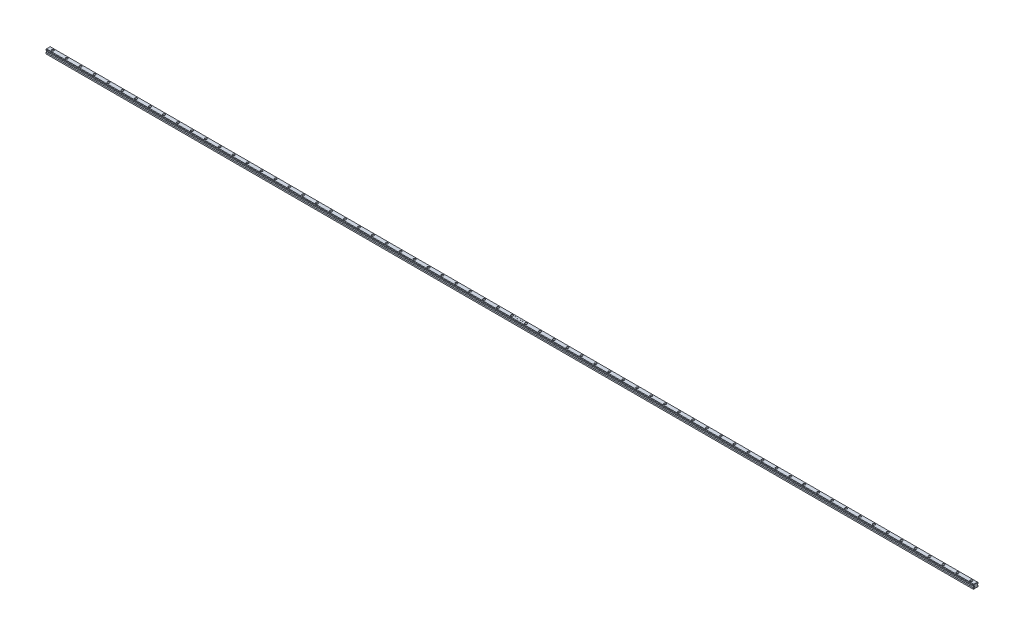
SolidWorks part; units mm, degrees
ref_plane "Front Plane" through (0, 0, 0) normal (0, 0, 1) x (1, 0, 0)
ref_plane "Top Plane" through (0, 0, 0) normal (0, 1, 0) x (1, 0, 0)
ref_plane "Right Plane" through (0, 0, 0) normal (1, 0, 0) x (0, 0, -1)
sketch "Sketch1" plane through (0, 0, 0) normal (1, 0, 0) x (0, 0, -1)
  line L0 (-10, 0) -> (10, 0)
  line L1 (-8, 18) -> (8, 18)
  line L2 (-10, 6) -> (-10, 0)
  line L3 (-8, 18) -> (-10, 16)
  line L4 (-10, 16) -> (-10, 13)
  line L5 (-10, 13) -> (-7, 10)
  line L6 (-7, 10) -> (-7, 8)
  line L7 (-7, 8) -> (-10, 6)
  line L8 (0, 0) -> (0, 18.5989) construction
  line L9 (-10, 18) -> (10, 18) construction
  line L10 (-10, 0) -> (10, 0) construction
  line L11 (10, 6) -> (10, 0)
  line L12 (7, 8) -> (10, 6)
  line L13 (7, 10) -> (7, 8)
  line L14 (10, 13) -> (7, 10)
  line L15 (10, 16) -> (10, 13)
  line L16 (8, 18) -> (10, 16)
  point P21 (0, 18)
  dimension "D3" = 6
  dimension "D4" = 2
  dimension "D5" = 2
  dimension "D6" = 3
  dimension "D7" = 3
  dimension "D8" = 2
  dimension "D9" = 3
  dimension "D2" = 18
extrude "Boss-Extrude1" add sketch "Sketch1" along normal blind 4000
chamfer "Chamfer1" distance 1 angle 45 14 edges at (0, 0, 0) (0, 3, -10) (0, 7, -8.5) (0, 9, -7) (0, 11.5, -8.5) (0, 14.5, -10) (0, 17, -9) (0, 18, 0) (0, 17, 9) (0, 14.5, 10) (0, 11.5, 8.5) (0, 9, 7) (0, 7, 8.5) (0, 3, 10)
chamfer "Chamfer2" distance 1 angle 45 14 edges at (4000, 7, 8.5) (4000, 9, 7) (4000, 11.5, 8.5) (4000, 14.5, 10) (4000, 17, 9) (4000, 18, 0) (4000, 17, -9) (4000, 14.5, -10) (4000, 11.5, -8.5) (4000, 9, -7) (4000, 7, -8.5) (4000, 3, -10) (4000, 0, 0) (4000, 3, 10)
sketch "Sketch2" plane through (0, 18, 0) normal (0, 1, 0) x (1, 0, 0)
  line L0 (4000, 7.5858) -> (4000, -7.5858) construction
  circle A0 centre (3980, 0) radius 4.75
  dimension "D2" = 9.5
  dimension "D1" = 20
extrude "Cut-Extrude1" cut sketch "Sketch2" against normal blind 8.5
sketch "Sketch3" plane through (0, 9.5, 0) normal (0, 1, 0) x (1, 0, 0)
  circle A0 centre (3980, 0) radius 3
  dimension "D1" = 6
extrude "Cut-Extrude2" cut sketch "Sketch3" against normal through all
pattern_linear "LPattern1" count 67 spacing 60 along (-1, 0, 0) of "Cut-Extrude2", "Cut-Extrude1"
sketch "Sketch4" plane through (0, 18, 0) normal (0, 1, 0) x (1, 0, 0)
  text T0 "SHN 20 B" font "Century Gothic" height 3.5
extrude "Cut-Extrude3" cut sketch "Sketch4" against normal blind 2
